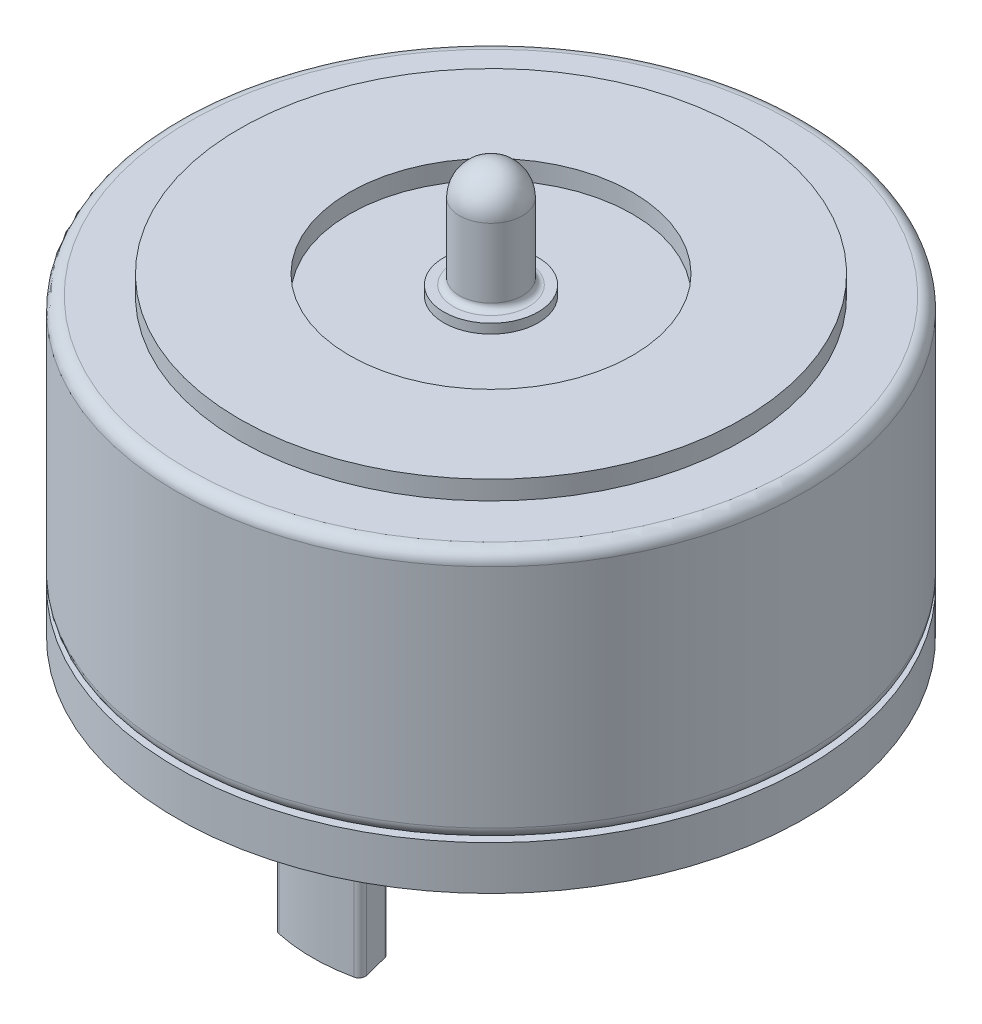
SolidWorks part; units mm, degrees
ref_plane "Спереди" through (0, 0, 0) normal (0, 0, 1) x (1, 0, 0)
ref_plane "Сверху" through (0, 0, 0) normal (0, 1, 0) x (1, 0, 0)
ref_plane "Справа" through (0, 0, 0) normal (1, 0, 0) x (0, 0, -1)
sketch "Эскиз1" plane through (0, 0, 0) normal (0, 1, 0) x (1, 0, 0)
  circle A0 centre (0, 0) radius 5
  dimension "D1" = 10
extrude "Бобышка-Вытянуть1" add sketch "Эскиз1" along normal blind 4.3
sketch "Эскиз2" plane through (0, 4.3, 0) normal (0, 1, 0) x (1, 0, 0)
  circle A0 centre (0, 0) radius 4
  circle A1 centre (0, 0) radius 2.25
  circle M1 centre (0, 0) radius 5
  dimension "D1" = 8
  dimension "D2" = 4.5
extrude "Вырез-Вытянуть1" cut sketch "Эскиз2" against normal blind 0.3 contours A0 M1 | A1
sketch "Эскиз3" plane through (0, 4, 0) normal (0, 1, 0) x (1, 0, 0)
  circle A0 centre (0, 0) radius 0.75
  dimension "D1" = 1.5
extrude "Бобышка-Вытянуть2" add sketch "Эскиз3" along normal blind 0.15
sketch "Эскиз4" plane through (0, 4.15, 0) normal (0, 1, 0) x (1, 0, 0)
  circle A0 centre (0, 0) radius 0.5
  dimension "D1" = 1
extrude "Бобышка-Вытянуть3" add sketch "Эскиз4" along normal blind 1.7
fillet "Скругление1" radius 0.5 1 edges at (0, 5.85, 0.5)
fillet "Скругление2" radius 0.2 2 edges at (0, 4, 5) (0, 0, 5)
fillet "Скругление3" radius 0.1 1 edges at (0, 4.15, 0.5)
sketch "Эскиз5" plane through (0, 0, 0) normal (0, -1, 0) x (1, 0, 0)
  circle A0 centre (0, 0) radius 5
  circle A1 centre (0, 0) radius 5 construction
extrude "Бобышка-Вытянуть4" add sketch "Эскиз5" along normal blind 0.7
sketch "Эскиз6" plane through (0, -0.7, 0) normal (0, -1, 0) x (1, 0, 0)
  line L0 (0, 0) -> (0, -4.065) construction
  line L1 (0, -3.6025) -> (0, 3.6025) construction
  line L2 (0.7, 2.7524) -> (0.5521, 2.1709)
  line L3 (-0.7, 2.7524) -> (-0.5521, 2.1709)
  line L4 (0.5521, -2.1709) -> (0.7, -2.7524)
  line L5 (-0.5521, -2.1709) -> (-0.7, -2.7524)
  circle A0 centre (0, 0) radius 2.54 construction
  arc A1 (-0.7, -2.7524) -> (0.7, -2.7524) centre (0, 0) ccw
  arc A2 (-0.5521, -2.1709) -> (0.5521, -2.1709) centre (0, 0) ccw
  arc A3 (0.7, 2.7524) -> (-0.7, 2.7524) centre (0, 0) ccw
  circle A4 centre (0, 0) radius 2.24 construction
  circle A5 centre (0, 0) radius 2.84 construction
  arc A6 (0.5521, 2.1709) -> (-0.5521, 2.1709) centre (0, 0) ccw
  point P6 (2.7159, 0.8303)
  point P19 (2.1421, 0.6549)
  dimension "D1" = 5.08
  dimension "D4" = 1.4
  dimension "D2" = 0.3
  dimension "D3" = 0.3
extrude "Бобышка-Вытянуть5" add sketch "Эскиз6" along normal blind 3
fillet "Скругление4" radius 0.1 8 edges at (0.7, -2.2, -2.7524) (-0.7, -2.2, -2.7524) (-0.5521, -2.2, -2.1709) (0.5521, -2.2, -2.1709) (0.7, -2.2, 2.7524) (0.5521, -2.2, 2.1709) (-0.7, -2.2, 2.7524) (-0.5521, -2.2, 2.1709)
sketch "Эскиз7" plane through (0, -0.7, 0) normal (0, -1, 0) x (1, 0, 0)
  circle A0 centre (0, 0) radius 0.3
  dimension "D1" = 0.6
extrude "Бобышка-Вытянуть6" add sketch "Эскиз7" along normal up to vertex (3 mm away)
